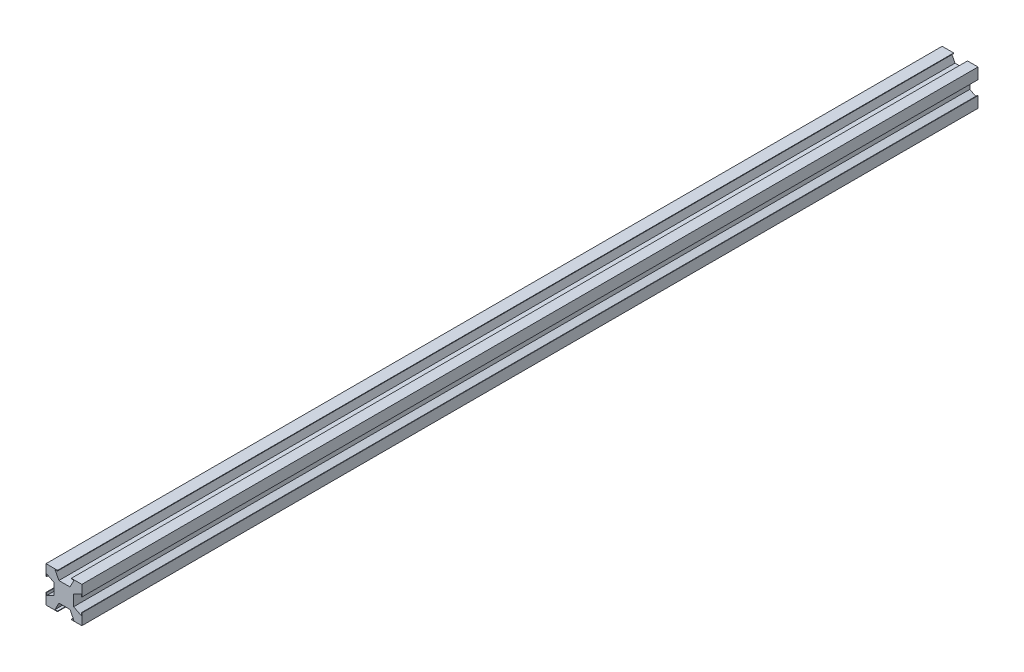
SolidWorks part; units mm, degrees
ref_plane "Ön Düzlem" through (0, 0, 0) normal (0, 0, 1) x (1, 0, 0)
ref_plane "Üst Düzlem" through (0, 0, 0) normal (0, 1, 0) x (1, 0, 0)
ref_plane "Sağ Düzlem" through (0, 0, 0) normal (1, 0, 0) x (0, 0, -1)
sketch "Çizim1" plane through (0, 0, 0) normal (0, 0, 1) x (1, 0, 0)
  line L0 (-5.1576, 10) -> (-2.803, 5.445)
  line L1 (-10, 10) -> (-5.1576, 10)
  line L2 (-10, 10) -> (-10, 5.45)
  line L3 (-10, -10) -> (-5.1576, -10)
  line L4 (10, 10) -> (10, 5.45)
  line L5 (-10, 10) -> (10, -10) construction
  line L6 (-10, -10) -> (10, 10) construction
  line L7 (-2.803, 5.445) -> (3.3917, 5.445)
  line L8 (10, 5.45) -> (5.4451, 3.095)
  line L9 (5.7462, 10) -> (3.3917, 5.445)
  line L10 (5.7462, 10) -> (10, 10)
  line L11 (5.4451, 3.095) -> (5.4451, -3.095)
  line L12 (5.7462, -10) -> (3.3917, -5.445)
  line L13 (-2.803, -5.445) -> (3.3917, -5.445)
  line L14 (-5.1576, -10) -> (-2.803, -5.445)
  line L15 (5.7462, -10) -> (10, -10)
  line L16 (5.4451, -3.095) -> (10, -5.45)
  line L17 (0, 2.2406) -> (0, -12.6593) construction
  line L18 (-5.4451, -3.095) -> (-10, -5.45)
  line L19 (-5.4451, 3.095) -> (-5.4451, -3.095)
  line L20 (-10, 5.45) -> (-5.4451, 3.095)
  line L21 (-10, -5.45) -> (-10, -10)
  line L22 (10, -5.45) -> (10, -10)
  point P0 (0, 0)
  point P12 (0.2943, 5.445)
  dimension "D1" = 20
  dimension "D2" = 20
  dimension "D3" = 6.19
  dimension "D4" = 4.55
  dimension "D5" = 4.55
  dimension "D6" = 117.34
  dimension "D7" = 117.34
extrude "Yükseklik-Ekstrüzyon1" add sketch "Çizim1" along normal blind 500
sketch "Çizim4" plane through (0, 0, 500) normal (0, 0, 1) x (1, 0, 0)
  line L0 (-5.1576, 10) -> (-3.55, 10)
  line L1 (-3.55, 10) -> (-3.55, 9.7051)
  line L2 (-3.55, 9.7051) -> (-5.0052, 9.7051)
  line L3 (-2.803, 5.445) -> (-5.1576, 10) construction
  line L4 (-5.0052, 9.7051) -> (-5.1576, 10)
  line L6 (10, 3.84) -> (9.71, 3.84)
  line L7 (5.5938, 9.7051) -> (5.7462, 10)
  line L8 (4.1386, 9.7051) -> (5.5938, 9.7051)
  line L9 (4.1386, 10) -> (4.1386, 9.7051)
  line L10 (5.7462, 10) -> (4.1386, 10)
  line L11 (-6.9605, 0) -> (11.3985, 0) construction
  line L12 (5.7462, -10) -> (4.1386, -10)
  line L13 (4.1386, -10) -> (4.1386, -9.7051)
  line L14 (4.1386, -9.7051) -> (5.5938, -9.7051)
  line L15 (5.5938, -9.7051) -> (5.7462, -10)
  line L16 (-5.0052, -9.7051) -> (-5.1576, -10)
  line L17 (-3.55, -9.7051) -> (-5.0052, -9.7051)
  line L18 (-3.55, -10) -> (-3.55, -9.7051)
  line L19 (-5.1576, -10) -> (-3.55, -10)
  line L20 (-10, 5.45) -> (-10, 3.84)
  line L21 (-10, 3.84) -> (-9.71, 3.84)
  line L22 (-9.71, 3.84) -> (-9.71, 5.3001)
  line L23 (-10, 5.45) -> (-5.4451, 3.095) construction
  line L24 (-9.71, 5.3001) -> (-10, 5.45)
  line L25 (10, 5.45) -> (10, 3.84)
  line L26 (9.71, 3.84) -> (9.71, 5.3001)
  line L27 (5.4451, 3.095) -> (10, 5.45) construction
  line L28 (9.71, 5.3001) -> (10, 5.45)
  line L29 (9.71, -5.3001) -> (10, -5.45)
  line L30 (9.71, -3.84) -> (9.71, -5.3001)
  line L31 (10, -5.45) -> (10, -3.84)
  line L32 (10, -3.84) -> (9.71, -3.84)
  line L33 (-9.71, -5.3001) -> (-10, -5.45)
  line L34 (-9.71, -3.84) -> (-9.71, -5.3001)
  line L35 (-10, -3.84) -> (-9.71, -3.84)
  line L36 (-10, -5.45) -> (-10, -3.84)
  point P11 (0.2943, 5.445)
  dimension "D1" = 1.6076
  dimension "D2" = 1.61
  dimension "D3" = 0.29
  dimension "D4" = 0.29
  dimension "D5" = 1.61
extrude "Yükseklik-Ekstrüzyon3" add sketch "Çizim4" against normal up to surface (500 mm away) up to face at (0.1177, 0, 0)
